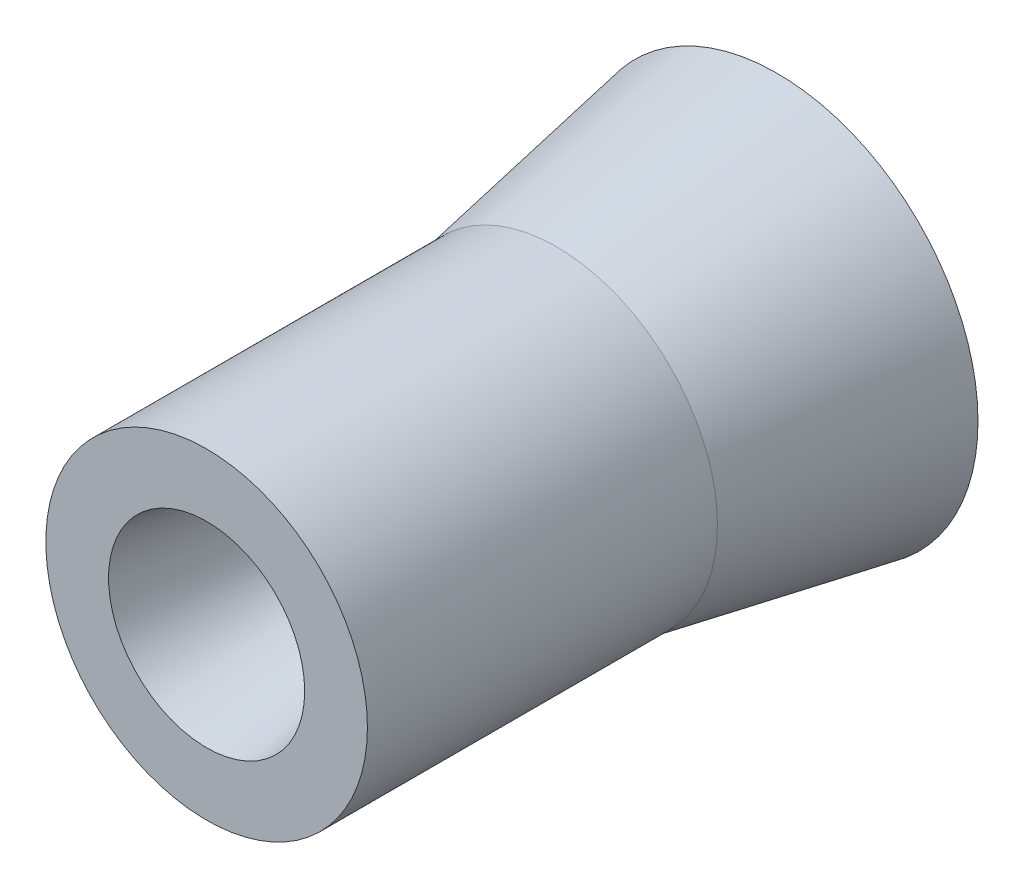
SolidWorks part; units mm, degrees
ref_plane "Front Plane" through (0, 0, 0) normal (0, 0, 1) x (1, 0, 0)
ref_plane "Top Plane" through (0, 0, 0) normal (0, 1, 0) x (1, 0, 0)
ref_plane "Right Plane" through (0, 0, 0) normal (1, 0, 0) x (0, 0, -1)
sketch "Sketch1" plane through (0, 0, 0) normal (1, 0, 0) x (0, 0, -1)
  line L0 (358.4801, 883.5084) -> (1791.1468, 883.5084) construction
  line L1 (1958.8047, 674.4008) -> (2053.3753, 658.9256)
  line L2 (2142.7875, 318.527) -> (2248.5003, 318.527)
  line L3 (2754.6337, 318.527) -> (-2754.6337, 318.527) construction
  line L4 (2326.7703, 318.527) -> (2428.4183, 318.527)
  line L5 (2509.0337, 318.527) -> (2602.4305, 318.527)
  line L6 (2689.7359, 318.527) -> (2777.7379, 318.527)
  line L7 (3260.7251, 318.527) -> (3337.6959, 318.527)
  line L8 (3393.7223, 318.527) -> (3481.1654, 318.527)
  line L9 (3528.2904, 318.527) -> (3609.4502, 318.527)
  line L10 (2443.8262, 375.8815) -> (2443.8262, 343.1066)
  line L11 (2443.8262, 343.1066) -> (2542.8481, 324.9759)
  line L12 (2542.8481, 324.9759) -> (2733.9186, 324.9759)
  line L13 (2733.9186, 324.9759) -> (2888.7274, 375.8815)
  line L14 (2888.7274, 375.8815) -> (2888.7274, 406.5643)
  line L15 (2888.7274, 406.5643) -> (2719.9718, 375.8815)
  line L16 (2719.9718, 375.8815) -> (2443.8262, 375.8815)
  point P2 (1958.8047, 674.4008)
  point P3 (2053.3753, 658.9256)
  point P4 (2142.7875, 643.4505)
  point P5 (2235.6387, 631.4142)
  point P6 (2326.7703, 612.5001)
  point P7 (2417.902, 598.7444)
  point P8 (2509.0337, 584.9886)
  point P9 (2602.4305, 573.3641)
  point P10 (2689.7359, 554.4873)
  point P11 (2785.2998, 545.0489)
  point P12 (1971.2366, 318.527)
  point P31 (3252.9128, 531.4222)
  point P32 (3393.7223, 564.5982)
  point P33 (3528.2904, 591.7422)
ref_plane "Plane1" through (0, 318.527, 0) normal (0, 1, 0) x (1, 0, 0)
sketch "Sketch55" plane through (0, 0, 0) normal (0, 1, 0) x (1, 0, 0)
  line L0 (0, 3798.472) -> (0, 3692.0528)
sketch "Sketch56" plane through (0, 0, 0) normal (1, 0, 0) x (0, 0, -1)
  line L0 (1616.5654, 254.8529) -> (3129.917, 254.8529) construction
revolve "Revolve-Thin1" add sketch "Sketch1" angle 360 about L0
